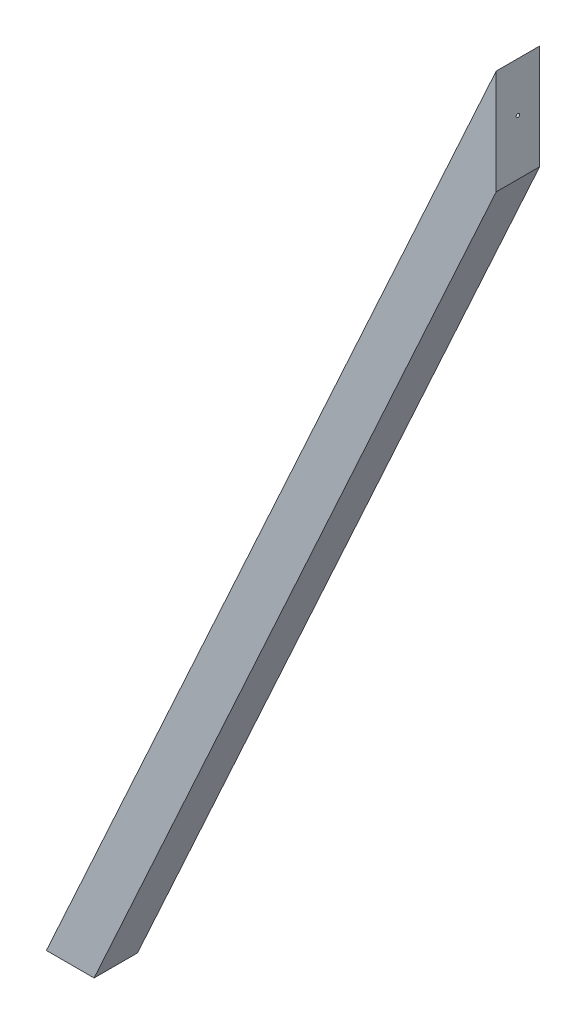
SolidWorks part; units mm, degrees
material "Pin"
ref_plane "Plan de face" through (0, 0, 0) normal (0, 0, 1) x (1, 0, 0)
ref_plane "Plan de dessus" through (0, 0, 0) normal (0, 1, 0) x (1, 0, 0)
ref_plane "Plan de droite" through (0, 0, 0) normal (1, 0, 0) x (0, 0, -1)
sketch "Esquisse1" plane through (0, 0, 0) normal (0, 0, 1) x (1, 0, 0)
  line L0 (-44, 1000) -> (-500, 0)
  line L4 (-44, 893.9502) -> (-44, 1000)
  line L9 (-451.6413, 0) -> (-44, 893.9502)
  line L11 (-451.6413, 0) -> (-500, 0) construction
  line L14 (-500, 0) -> (-451.6413, 0)
extrude "Boss.-Extru.1" add sketch "Esquisse1" along normal blind 44
sketch "Esquisse2" plane through (-44, 0, 0) normal (1, 0, 0) x (0, 0, -1)
  line L0 (-44, 893.9502) -> (-44, 1000) construction
  line L1 (-44, 1000) -> (0, 1000) construction
  circle A0 centre (-22, 950) radius 1.75
  dimension "D1" = 3.5
  dimension "D2" = 22
  dimension "D3" = 50
extrude "Enlèv. mat.-Extru.1" cut sketch "Esquisse2" against normal up to surface (22.002 mm away)
